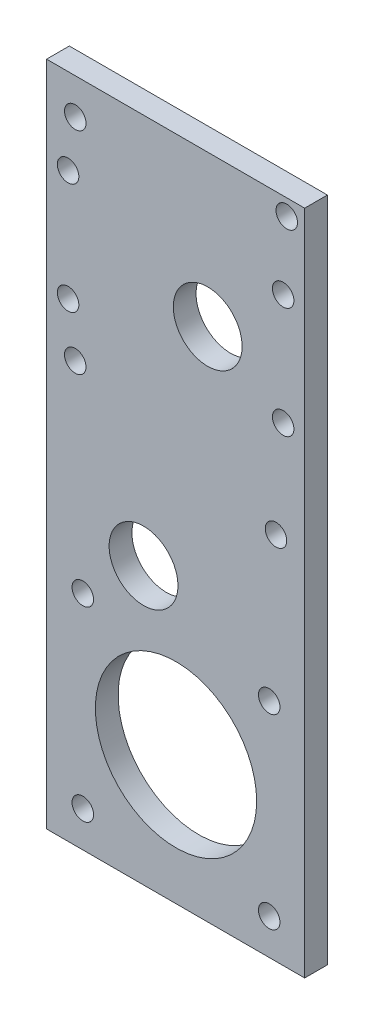
SolidWorks part; units mm, degrees
ref_plane "Front Plane" through (0, 0, 0) normal (0, 0, 1) x (1, 0, 0)
ref_plane "Top Plane" through (0, 0, 0) normal (0, 1, 0) x (1, 0, 0)
ref_plane "Right Plane" through (0, 0, 0) normal (1, 0, 0) x (0, 0, -1)
sketch "Sketch1" plane through (0, 0, 0) normal (0, 0, 1) x (1, 0, 0)
  line L0 (0, 0) -> (0, 33.3706) construction
  line L1 (0, 0) -> (-4.475, 0) construction
  line L2 (0, 0) -> (5.375, 0) construction
  line L3 (0, 33.3706) -> (4.475, 33.3706) construction
  line L4 (0, 0) -> (0, -33.0349) construction
  line L5 (0, 33.3706) -> (-5.375, 33.3706) construction
  circle A0 centre (4.475, 33.3706) radius 17.275 construction
  circle A1 centre (-4.475, 0) radius 17.275 construction
  circle A2 centre (-5.375, 33.3706) radius 2.5 construction
  circle A3 centre (0.0538, -20.5571) radius 3.775 construction
  circle A4 centre (5.375, 0) radius 2.5
  dimension "D3" = 5.375
  dimension "D1" = 4.475
  dimension "D2" = 5.375
  dimension "D4" = 4.475
sketch "Sketch2" plane through (0, 0, 0) normal (0, 0, 1) x (1, 0, 0)
  line L0 (0, 0) -> (0, 33.3706) construction
  line L1 (-12.9462, -33.5571) -> (13.0538, -33.5571) construction
  line L2 (-12.9462, -33.5571) -> (-12.9462, -7.5571) construction
  line L3 (-12.9462, -7.5571) -> (13.0538, -7.5571) construction
  line L4 (13.0538, -33.5571) -> (13.0538, -7.5571) construction
  line L5 (-12.9462, -33.5571) -> (13.0538, -7.5571) construction
  line L6 (-12.9462, -7.5571) -> (13.0538, -33.5571) construction
  line L7 (-18, 54.4429) -> (18, 54.4429)
  line L8 (-18, 54.4429) -> (-18, -38.5571)
  line L9 (-18, -38.5571) -> (18, -38.5571)
  line L10 (18, 54.4429) -> (18, -38.5571)
  line L11 (-18, 54.4429) -> (18, -38.5571) construction
  line L12 (-18, -38.5571) -> (18, 54.4429) construction
  circle A0 centre (13.0538, -33.5571) radius 1.5
  circle A1 centre (13.0538, -7.5571) radius 1.5
  circle A2 centre (-12.9462, -33.5571) radius 1.5
  circle A3 centre (-12.9462, -7.5571) radius 1.5
  circle A4 centre (0.0538, -20.5571) radius 11.25
  circle A5 centre (-4.475, 0) radius 4.8
  circle A6 centre (4.475, 33.3706) radius 4.8
  circle A7 centre (14, 13) radius 1.5
  circle A8 centre (-14, 20) radius 1.5
  circle A9 centre (-14, 49.4429) radius 1.5
  circle A10 centre (15.5, 52.1871) radius 1.5
  point P0 (0.0538, -20.5571)
  point P17 (0, 7.9429)
  dimension "D1" = 5
  dimension "D2" = 4
  dimension "D4" = 2.5
  dimension "D3" = 5
extrude "Boss-Extrude1" add sketch "Sketch2" along normal blind 3.175
sketch "Sketch3" plane through (0, 0, 3.175) normal (0, 0, 1) x (1, 0, 0)
  circle A0 centre (-15, 42.5) radius 1.5
  circle A1 centre (15, 42.5) radius 1.5
  circle A2 centre (-15, 27) radius 1.5
  circle A3 centre (15, 27) radius 1.5
  point P4 (0, 32.6678)
extrude "Cut-Extrude1" cut sketch "Sketch3" against normal blind 16
